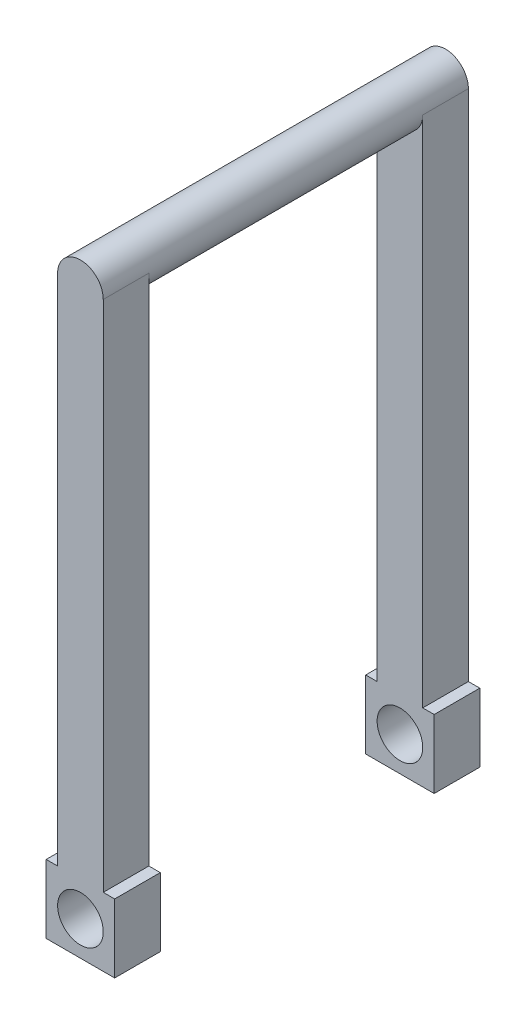
SolidWorks part; units mm, degrees
ref_plane "Front Plane" through (0, 0, 0) normal (0, 0, 1) x (1, 0, 0)
ref_plane "Top Plane" through (0, 0, 0) normal (0, 1, 0) x (1, 0, 0)
ref_plane "Right Plane" through (0, 0, 0) normal (1, 0, 0) x (0, 0, -1)
sketch "Sketch2" plane through (0, 0, 0) normal (0, 0, 1) x (1, 0, 0)
  circle A0 centre (0, 0) radius 6.35
  dimension "D1" = 12.7
extrude "Boss-Extrude1" add sketch "Sketch2" along normal blind 76.2
sketch "Sketch3" plane through (0, 0, 76.2) normal (0, 0, 1) x (1, 0, 0)
  line L1 (-6.35, 0) -> (6.35, 0)
  line L2 (-6.35, 0) -> (-6.35, -152.4)
  line L3 (-6.35, -152.4) -> (6.35, -152.4)
  line L4 (6.35, 0) -> (6.35, -152.4)
  circle A0 centre (0, 0) radius 6.35 construction
  dimension "D1" = 152.4
extrude "Boss-Extrude2" add sketch "Sketch3" along normal blind 12.7
sketch "Sketch4" plane through (0, 0, 76.2) normal (0, 0, 1) x (1, 0, 0)
  line L0 (6.35, 0) -> (-6.35, 0) construction
  line L1 (-6.35, 0) -> (6.35, 0)
  arc A0 (6.35, 0) -> (-6.35, 0) centre (0, 0) ccw
extrude "Boss-Extrude3" add sketch "Sketch4" along normal blind 12.7
sketch "Sketch6" plane through (0, 0, 0) normal (0, 0, -1) x (-1, 0, 0)
  line L0 (-6.35, 0) -> (6.35, 0)
  line L1 (-6.35, -152.4) -> (6.35, -152.4)
  line L2 (6.35, 0) -> (6.35, -152.4)
  line L3 (-6.35, -152.4) -> (-6.35, 0)
extrude "Boss-Extrude4" add sketch "Sketch6" along normal blind 12.7
sketch "Sketch7" plane through (0, 0, 0) normal (0, 0, -1) x (-1, 0, 0)
  line L0 (6.35, 0) -> (-6.35, 0) construction
  line L1 (-6.35, 0) -> (6.35, 0)
  arc A0 (6.35, 0) -> (-6.35, 0) centre (0, 0) ccw
extrude "Boss-Extrude5" add sketch "Sketch7" along normal blind 12.7
sketch "Sketch8" plane through (0, 0, -12.7) normal (0, 0, -1) x (-1, 0, 0)
  line L0 (-6.35, -152.4) -> (6.35, -152.4) construction
  line L1 (-9.525, -142.875) -> (9.525, -142.875)
  line L2 (-9.525, -142.875) -> (-9.525, -161.925)
  line L3 (-9.525, -161.925) -> (9.525, -161.925)
  line L4 (9.525, -142.875) -> (9.525, -161.925)
  line L5 (-9.525, -142.875) -> (9.525, -161.925) construction
  line L6 (-9.525, -161.925) -> (9.525, -142.875) construction
  point P0 (0, -152.4)
  dimension "D1" = 19.05
  dimension "D2" = 19.05
extrude "Boss-Extrude6" add sketch "Sketch8" against normal up to surface (101.6 mm away) up to face at (0, -74.6125, 88.9)
sketch "Sketch9" plane through (9.525, 0, 0) normal (1, 0, 0) x (0, 0, -1)
  line L1 (-76.2, -142.875) -> (0, -142.875)
  line L2 (-76.2, -142.875) -> (-76.2, -172.1948)
  line L3 (-76.2, -172.1948) -> (0, -172.1948)
  line L4 (0, -142.875) -> (0, -172.1948)
extrude "Cut-Extrude1" cut sketch "Sketch9" against normal blind 198.12
sketch "Sketch10" plane through (0, 0, 88.9) normal (0, 0, 1) x (1, 0, 0)
  line L0 (-9.525, -152.4) -> (9.525, -152.4)
  line L1 (-9.525, -161.925) -> (-9.525, -142.875) construction
  line L2 (9.525, -142.875) -> (9.525, -161.925) construction
  circle A0 centre (0, -152.4) radius 6.35
  dimension "D1" = 12.7
extrude "Cut-Extrude2" cut sketch "Sketch10" against normal through all contours L0 A0 | L0 A0
